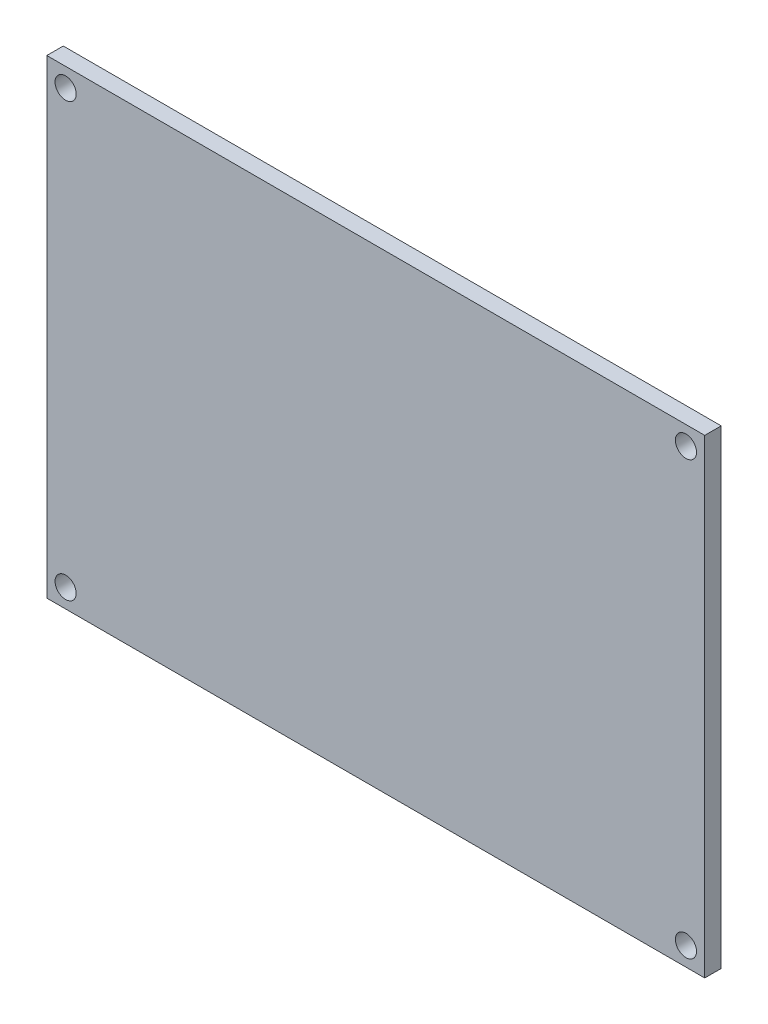
SolidWorks part; units mm, degrees
ref_plane "Front" through (0, 0, 0) normal (0, 0, 1) x (1, 0, 0)
ref_plane "Top" through (0, 0, 0) normal (0, 1, 0) x (1, 0, 0)
ref_plane "Right" through (0, 0, 0) normal (1, 0, 0) x (0, 0, -1)
sketch "Sketch1" plane through (0, 0, 0) normal (0, 0, 1) x (1, 0, 0)
  line L1 (-35, -25) -> (35, -25)
  line L2 (-35, -25) -> (-35, 25)
  line L3 (-35, 25) -> (35, 25)
  line L4 (35, -25) -> (35, 25)
  line L5 (-35, -25) -> (35, 25) construction
  line L6 (-35, 25) -> (35, -25) construction
  line L7 (-33, -23) -> (33, -23) construction
  line L8 (-33, -23) -> (-33, 23) construction
  line L9 (-33, 23) -> (33, 23) construction
  line L10 (33, -23) -> (33, 23) construction
  line L11 (-33, -23) -> (33, 23) construction
  line L12 (-33, 23) -> (33, -23) construction
  circle A0 centre (-33, 23) radius 1.125
  circle A1 centre (33, 23) radius 1.125
  circle A2 centre (33, -23) radius 1.125
  circle A3 centre (-33, -23) radius 1.125
  point P0 (0, 0)
  point P6 (0, 0)
  dimension "D5" = 2.25
  dimension "D1" = 70
  dimension "D2" = 50
  dimension "D3" = 46
  dimension "D4" = 66
extrude "Boss-Extrude1" add sketch "Sketch1" along normal blind 1.75
